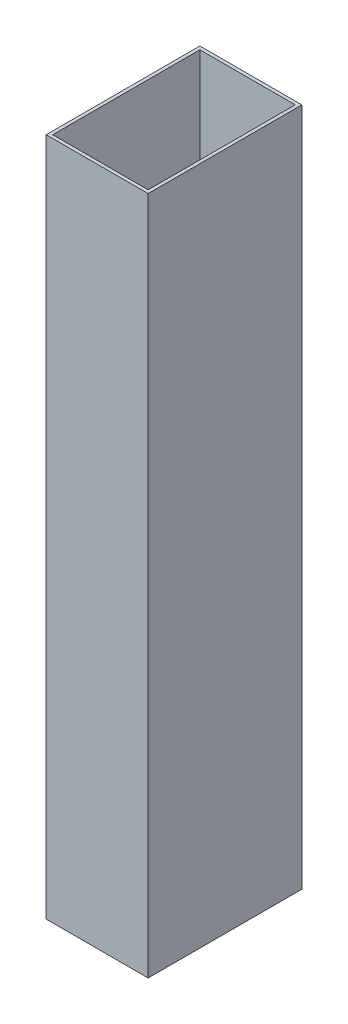
SolidWorks part; units mm, degrees
material "Acrílico (Impacto medio-alto)"
ref_plane "Alzado" through (0, 0, 0) normal (0, 0, 1) x (1, 0, 0)
ref_plane "Planta" through (0, 0, 0) normal (0, 1, 0) x (1, 0, 0)
ref_plane "Vista lateral" through (0, 0, 0) normal (1, 0, 0) x (0, 0, -1)
sketch "Croquis1" plane through (0, 0, 0) normal (0, 1, 0) x (1, 0, 0)
  line L0 (29.5, 45.5) -> (29.5, -45.5)
  line L1 (31.5, 47.5) -> (-31.5, 47.5)
  line L2 (31.5, 47.5) -> (31.5, -47.5)
  line L3 (31.5, -47.5) -> (-31.5, -47.5)
  line L4 (-31.5, 47.5) -> (-31.5, -47.5)
  line L5 (31.5, 47.5) -> (-31.5, -47.5) construction
  line L6 (31.5, -47.5) -> (-31.5, 47.5) construction
  line L7 (29.5, -45.5) -> (-29.5, -45.5)
  line L8 (-29.5, 45.5) -> (-29.5, -45.5)
  line L9 (29.5, 45.5) -> (-29.5, 45.5)
  point P0 (0, 0)
  dimension "D1" = 95
  dimension "D2" = 63
  dimension "D3" = 2
extrude "Saliente-Extruir1" add sketch "Croquis1" along normal blind 420
